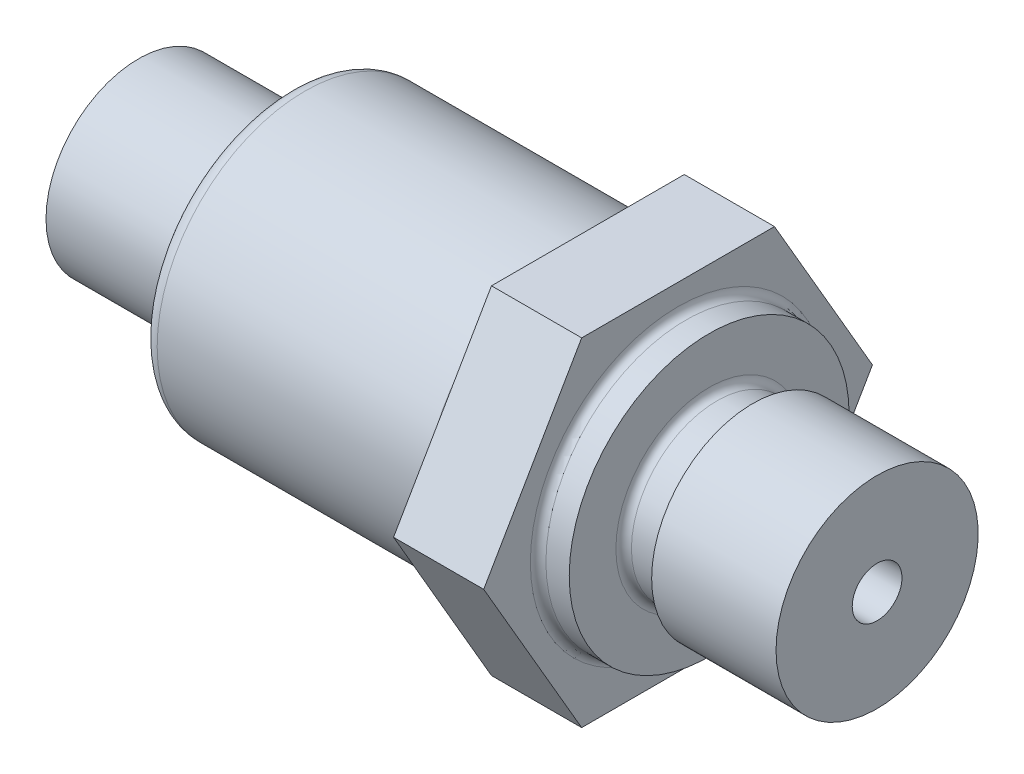
SolidWorks part; units mm, degrees
ref_plane "Plane1" through (0, 0, 0) normal (0, 0, 1) x (1, 0, 0)
ref_plane "Plane2" through (0, 0, 0) normal (0, 1, 0) x (1, 0, 0)
ref_plane "Plane3" through (0, 0, 0) normal (1, 0, 0) x (0, 0, -1)
sketch "Sketch1" plane through (0, 0, 0) normal (0, 0, 1) x (1, 0, 0)
  line L0 (0, 0) -> (58.6144, 0) construction
  line L1 (0, 4.1) -> (0, 5.95)
  line L2 (0, 5.95) -> (9.7, 5.95)
  line L3 (9.7, 5.95) -> (9.7, 8.5)
  line L4 (10.7, 9.5) -> (27.9, 9.5)
  line L5 (28.9, 10.5) -> (28.9, 12.5)
  line L6 (28.9, 12.5) -> (34.7, 12.5)
  line L7 (34.7, 12.5) -> (34.7, 9.5)
  line L8 (35.2, 9) -> (36.7, 9)
  line L9 (36.7, 9) -> (36.7, 6.5)
  line L10 (39.5, 6.5) -> (47.5, 6.5)
  line L11 (47.5, 6.5) -> (47.5, 1.6)
  line L12 (32.5, 0) -> (9.4, 0)
  line L13 (0, 4.1) -> (9.4, 4.1)
  line L14 (9.4, 4.1) -> (9.4, 0)
  line L15 (36.7, 6.5) -> (36.7, 6)
  line L16 (37.2, 5.5) -> (39, 5.5)
  line L17 (39.5, 6) -> (39.5, 6.5)
  line L18 (47.5, 1.6) -> (32.5, 1.6)
  line L19 (32.5, 1.6) -> (32.5, 0)
  arc A0 (27.9, 9.5) -> (28.9, 10.5) centre (27.9, 10.5) ccw
  arc A1 (36.7, 6) -> (37.2, 5.5) centre (37.2, 6) ccw
  arc A2 (39, 5.5) -> (39.5, 6) centre (39, 6) ccw
  arc A3 (34.7, 9.5) -> (35.2, 9) centre (35.2, 9.5) ccw
  arc A4 (9.7, 8.5) -> (10.7, 9.5) centre (10.7, 8.5) cw
  dimension "D15" = 1
  dimension "D16" = 0.5
  dimension "D17" = 1
  dimension "D1" = 47.5
  dimension "D2" = 10.8
  dimension "D3" = 2
  dimension "D4" = 5.8
  dimension "D5" = 19.2
  dimension "D6" = 11.9
  dimension "D7" = 19
  dimension "D8" = 25
  dimension "D9" = 18
  dimension "D10" = 13
  dimension "D11" = 8.2
  dimension "D12" = 9.4
  dimension "D13" = 2.8
  dimension "D14" = 11
  dimension "D18" = 3.2
  dimension "D19" = 15
revolve "Revolve1" add sketch "Sketch1" angle 360 about L0
sketch "Sketch2" plane through (28.9, 0, 0) normal (1, 0, 0) x (0, 0, -1)
  line L0 (-12.5, 0) -> (12.5, 0) construction
  line L1 (0, 0) -> (6.2, -10.854) construction
  line L2 (6.2, -10.854) -> (0, 0) construction
  line L3 (0, 0) -> (-6.2, -10.854) construction
  line L4 (0, 0) -> (-6.2, 10.854) construction
  line L5 (0, 0) -> (6.2, 10.854) construction
  line L6 (6.2, 10.854) -> (12.5, 0)
  line L7 (12.5, 0) -> (6.2, -10.854)
  line L8 (6.2, -10.854) -> (-6.2, -10.854)
  line L9 (-6.2, -10.854) -> (-12.5, 0)
  line L10 (-12.5, 0) -> (-6.2, 10.854)
  line L11 (-6.2, 10.854) -> (6.2, 10.854)
  circle A0 centre (0, 0) radius 12.5 construction
  dimension "D1" = 12.4
extrude "Cut-Extrude1" cut sketch "Sketch2" along normal up to surface (5.8 mm away) flip side to cut up to face at (34.7, 0, 12.5)
